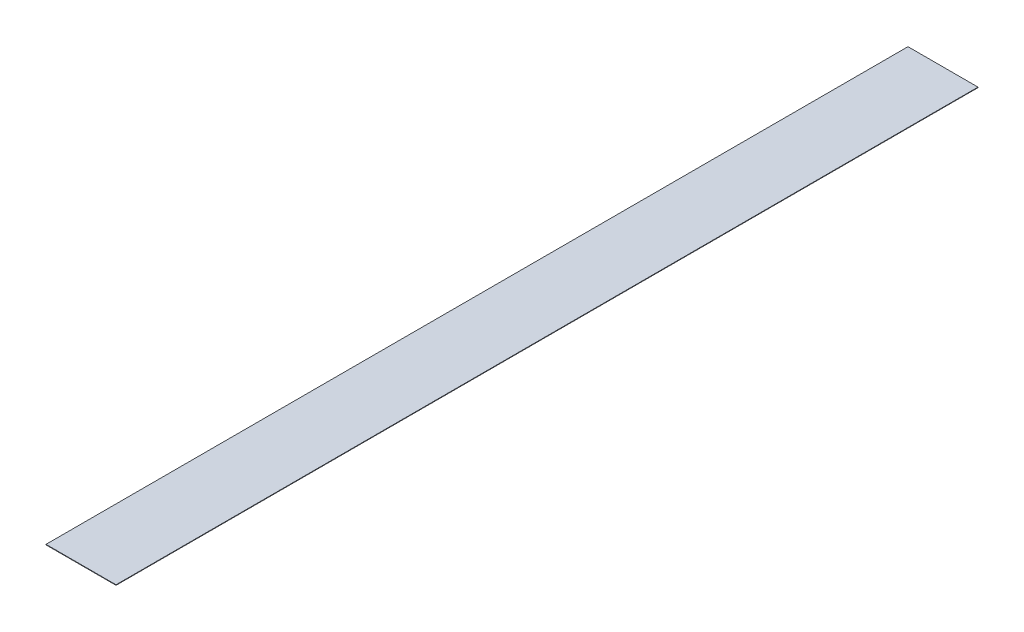
SolidWorks part; units mm, degrees
material "ladder carbon corrected"
ref_plane "Front" through (0, 0, 0) normal (0, 0, 1) x (1, 0, 0)
ref_plane "Top" through (0, 0, 0) normal (0, 1, 0) x (1, 0, 0)
ref_plane "Right" through (0, 0, 0) normal (1, 0, 0) x (0, 0, -1)
sketch "Sketch1" plane through (0, 0, 0) normal (0, 1, 0) x (1, 0, 0)
  line L0 (12.45, 153.25) -> (-12.45, -153.25) construction
  line L1 (-12.45, 153.25) -> (12.45, 153.25)
  line L2 (-12.45, 153.25) -> (-12.45, -153.25)
  line L3 (-12.45, -153.25) -> (12.45, -153.25)
  line L4 (12.45, 153.25) -> (12.45, -153.25)
  point P4 (0, 0)
  dimension "D1" = 306.5
  dimension "D2" = 24.9
extrude "Extrude1" add sketch "Sketch1" along normal blind 0.175
